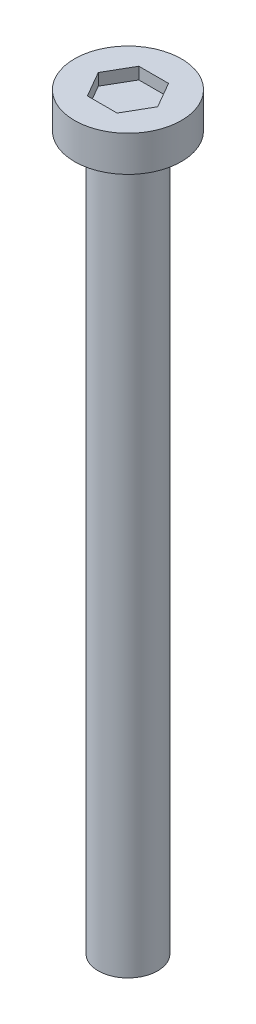
SolidWorks part; units mm, degrees
ref_plane "Front Plane" through (0, 0, 0) normal (0, 0, 1) x (1, 0, 0)
ref_plane "Top Plane" through (0, 0, 0) normal (0, 1, 0) x (1, 0, 0)
ref_plane "Right Plane" through (0, 0, 0) normal (1, 0, 0) x (0, 0, -1)
sketch "Sketch1" plane through (0, 0, 0) normal (0, 1, 0) x (1, 0, 0)
  circle A0 centre (0, 0) radius 1.25
  dimension "D1" = 2.5
extrude "Boss-Extrude1" add sketch "Sketch1" along normal blind 30
sketch "Sketch4" plane through (0, 30, 0) normal (0, 1, 0) x (1, 0, 0)
  circle A0 centre (0, 0) radius 2.25
  dimension "D1" = 4.5
extrude "Boss-Extrude2" add sketch "Sketch4" along normal blind 1.5
sketch "Sketch5" plane through (0, 31.5, 0) normal (0, 1, 0) x (1, 0, 0)
  line L1 (1.25, 0) -> (0.625, 1.0825)
  line L2 (0.625, 1.0825) -> (-0.625, 1.0825)
  line L3 (-0.625, 1.0825) -> (-1.25, 0)
  line L4 (-1.25, 0) -> (-0.625, -1.0825)
  line L5 (-0.625, -1.0825) -> (0.625, -1.0825)
  line L6 (0.625, -1.0825) -> (1.25, 0)
  circle A0 centre (0, 0) radius 1.0825 construction
  dimension "D1" = 1.25
extrude "Cut-Extrude1" cut sketch "Sketch5" against normal blind 0.5
thread "Thread1" pitch 0.7 start angle 0, offset 0, length 28, pitch 0.7, diameter 2.5
ref_plane "Plane1" through (1.25, 0, 0) normal (0, 0, 1) x (1, 0, 0)
sketch "Thread Profile1" plane through (1.25, 0, 0) normal (0, 0, 1) x (1, 0, 0)
  line L0 (0, 0) -> (0, 0.7) construction
  line L1 (0, 0) -> (0.3789, 0.2187)
  line L2 (0.3789, 0.2187) -> (0.3789, 0.3062)
  line L3 (0.3789, 0.3062) -> (0, 0.525)
  line L4 (0.3789, 0.2625) -> (0, 0.2625) construction
  line L11 (0, 0) -> (0, 0.525)
  point P2 (0, 0)
  dimension "Pitch" = 0.7
  dimension "Profile_Angle" = 60
  dimension "Profile_Land" = 0.0875
  dimension "Profile_Height" = 0.3789
